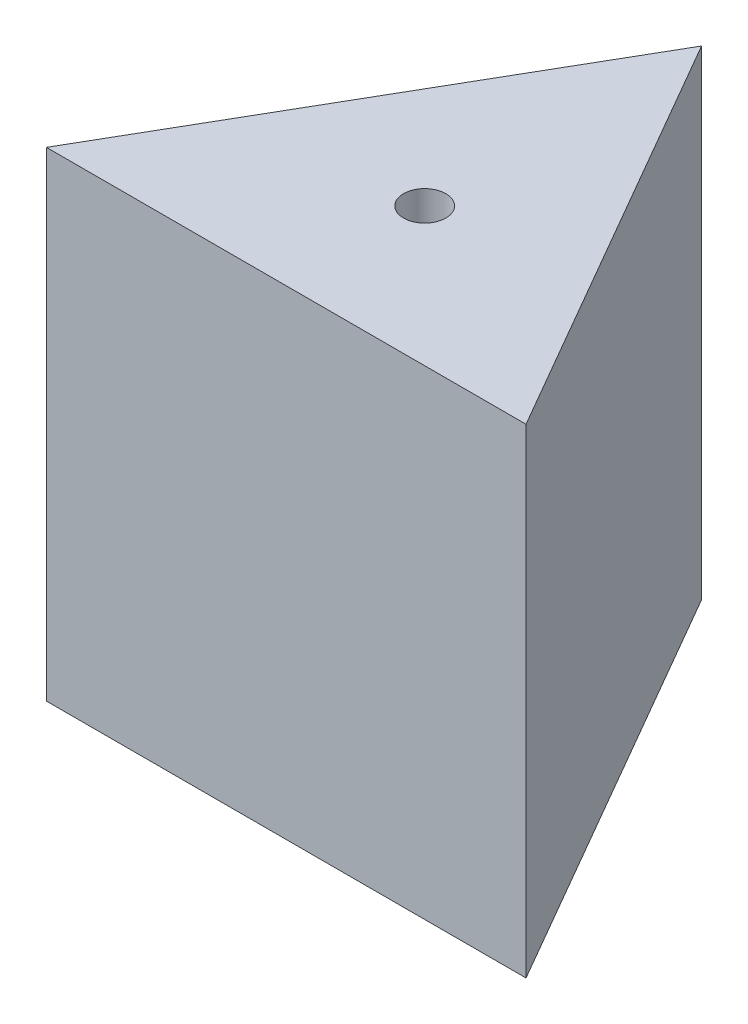
SolidWorks part; units mm, degrees
ref_plane "Front Plane" through (0, 0, 0) normal (0, 0, 1) x (1, 0, 0)
ref_plane "Top Plane" through (0, 0, 0) normal (0, 1, 0) x (1, 0, 0)
ref_plane "Right Plane" through (0, 0, 0) normal (1, 0, 0) x (0, 0, -1)
sketch "Sketch1" plane through (0, 0, 0) normal (0, 1, 0) x (1, 0, 0)
  line L0 (0, 0) -> (-215.9, -373.9498)
  line L1 (-215.9, -373.9498) -> (215.9, -373.9498)
  line L2 (215.9, -373.9498) -> (0, 0)
extrude "Boss-Extrude1" add sketch "Sketch1" along normal blind 431.8
sketch "Sketch2" plane through (0, 431.8, 0) normal (0, 1, 0) x (1, 0, 0)
  line L0 (0, 0) -> (0, -373.9498) construction
  line L1 (-215.9, -373.9498) -> (215.9, -373.9498) construction
  line L2 (-215.9, -373.9498) -> (107.95, -186.9749) construction
  line L3 (215.9, -373.9498) -> (0, 0) construction
  circle A0 centre (0, -249.2998) radius 19.05
extrude "Cut-Extrude1" cut sketch "Sketch2" against normal through all
sketch "Sketch3" plane through (0, 431.8, 0) normal (0, 1, 0) x (1, 0, 0)
  line L0 (0, 0) -> (0, -230.2498)
  line L1 (0, -268.3498) -> (0, -373.9498)
  line L2 (-215.9, -373.9498) -> (215.9, -373.9498) construction
  circle A0 centre (0, -249.2998) radius 19.05 construction
